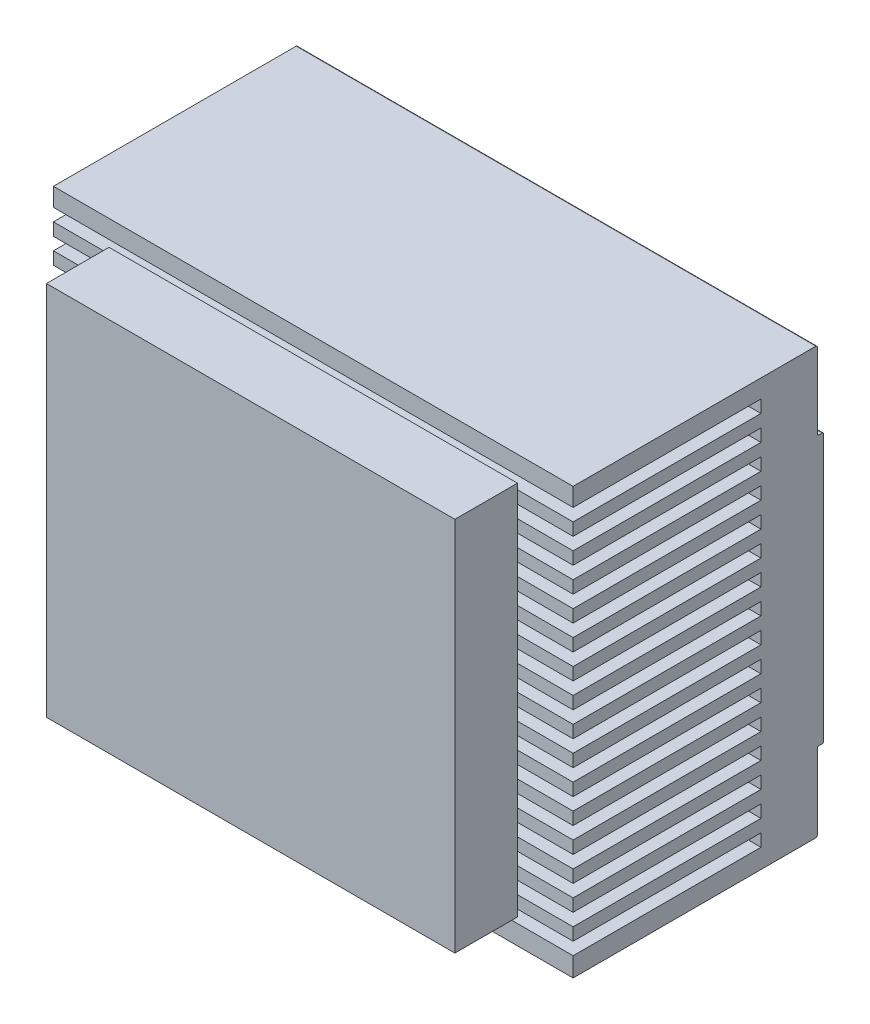
SolidWorks part; units mm, degrees
ref_plane "Front Plane" through (0, 0, 0) normal (0, 0, 1) x (1, 0, 0)
ref_plane "Top Plane" through (0, 0, 0) normal (0, 1, 0) x (1, 0, 0)
ref_plane "Right Plane" through (0, 0, 0) normal (1, 0, 0) x (0, 0, -1)
sketch "Sketch1" plane through (0, 0, 0) normal (0, 0, 1) x (1, 0, 0)
  line L1 (0, 0) -> (83, 0)
  line L2 (0, 0) -> (0, 68)
  line L3 (0, 68) -> (83, 68)
  line L4 (83, 0) -> (83, 68)
  dimension "D1" = 83
  dimension "D2" = 68
extrude "Boss-Extrude1" add sketch "Sketch1" along normal blind 40
sketch "Sketch2" plane through (0, 0, 40) normal (0, 0, 1) x (1, 0, 0)
  line L0 (8.8849, 64) -> (0, 68) construction
  line L1 (8.8849, 64) -> (74.1151, 64)
  line L2 (8.8849, 64) -> (8.8849, 4)
  line L3 (8.8849, 4) -> (74.1151, 4)
  line L4 (74.1151, 64) -> (74.1151, 4)
  line L5 (74.1151, 4) -> (83, 0) construction
  dimension "D1" = 60
extrude "Boss-Extrude2" add sketch "Sketch2" along normal blind 10 separate body
sketch "Sketch3" plane through (0, 0, 40) normal (0, 0, 1) x (1, 0, 0)
  line L0 (0, 68) -> (0, 0) construction
  line L1 (0, 65.0818) -> (83, 65.0818)
  line L2 (0, 65.0818) -> (0, 63.0818)
  line L3 (0, 63.0818) -> (83, 63.0818)
  line L4 (83, 65.0818) -> (83, 63.0818)
  line L5 (83, 0) -> (83, 68) construction
  line L6 (0, 61.0818) -> (0, 59.0818)
  line L7 (0, 61.0818) -> (83, 61.0818)
  line L8 (83, 61.0818) -> (83, 59.0818)
  line L9 (0, 59.0818) -> (83, 59.0818)
  line L10 (0, 57.0818) -> (0, 55.0818)
  line L11 (0, 57.0818) -> (83, 57.0818)
  line L12 (83, 57.0818) -> (83, 55.0818)
  line L13 (0, 55.0818) -> (83, 55.0818)
  line L14 (0, 53.0818) -> (0, 51.0818)
  line L15 (0, 53.0818) -> (83, 53.0818)
  line L16 (83, 53.0818) -> (83, 51.0818)
  line L17 (0, 51.0818) -> (83, 51.0818)
  line L18 (0, 49.0818) -> (0, 47.0818)
  line L19 (0, 49.0818) -> (83, 49.0818)
  line L20 (83, 49.0818) -> (83, 47.0818)
  line L21 (0, 47.0818) -> (83, 47.0818)
  line L22 (0, 45.0818) -> (0, 43.0818)
  line L23 (0, 45.0818) -> (83, 45.0818)
  line L24 (83, 45.0818) -> (83, 43.0818)
  line L25 (0, 43.0818) -> (83, 43.0818)
  line L26 (0, 41.0818) -> (0, 39.0818)
  line L27 (0, 41.0818) -> (83, 41.0818)
  line L28 (83, 41.0818) -> (83, 39.0818)
  line L29 (0, 39.0818) -> (83, 39.0818)
  line L30 (0, 37.0818) -> (0, 35.0818)
  line L31 (0, 37.0818) -> (83, 37.0818)
  line L32 (83, 37.0818) -> (83, 35.0818)
  line L33 (0, 35.0818) -> (83, 35.0818)
  line L34 (0, 33.0818) -> (0, 31.0818)
  line L35 (0, 33.0818) -> (83, 33.0818)
  line L36 (83, 33.0818) -> (83, 31.0818)
  line L37 (0, 31.0818) -> (83, 31.0818)
  line L38 (0, 29.0818) -> (0, 27.0818)
  line L39 (0, 29.0818) -> (83, 29.0818)
  line L40 (83, 29.0818) -> (83, 27.0818)
  line L41 (0, 27.0818) -> (83, 27.0818)
  line L42 (0, 25.0818) -> (0, 23.0818)
  line L43 (0, 25.0818) -> (83, 25.0818)
  line L44 (83, 25.0818) -> (83, 23.0818)
  line L45 (0, 23.0818) -> (83, 23.0818)
  line L46 (0, 21.0818) -> (0, 19.0818)
  line L47 (0, 21.0818) -> (83, 21.0818)
  line L48 (83, 21.0818) -> (83, 19.0818)
  line L49 (0, 19.0818) -> (83, 19.0818)
  line L50 (0, 17.0818) -> (0, 15.0818)
  line L51 (0, 17.0818) -> (83, 17.0818)
  line L52 (83, 17.0818) -> (83, 15.0818)
  line L53 (0, 15.0818) -> (83, 15.0818)
  line L54 (0, 13.0818) -> (0, 11.0818)
  line L55 (0, 13.0818) -> (83, 13.0818)
  line L56 (83, 13.0818) -> (83, 11.0818)
  line L57 (0, 11.0818) -> (83, 11.0818)
  line L58 (0, 9.0818) -> (0, 7.0818)
  line L59 (0, 9.0818) -> (83, 9.0818)
  line L60 (83, 9.0818) -> (83, 7.0818)
  line L61 (0, 7.0818) -> (83, 7.0818)
  line L62 (0, 5.0818) -> (0, 3.0818)
  line L63 (0, 5.0818) -> (83, 5.0818)
  line L64 (83, 5.0818) -> (83, 3.0818)
  line L65 (0, 3.0818) -> (83, 3.0818)
  dimension "D1" = 2
  dimension "D2" = 16
extrude "Cut-Extrude1" cut sketch "Sketch3" against normal offset from surface (30 mm away) 10 up to face at (41.5, 34, 0)
sketch "Sketch4" plane through (0, 0, 0) normal (0, 0, -1) x (-1, 0, 0)
  line L0 (0, 68) -> (0, 0) construction
  line L1 (-83, 68) -> (0, 68)
  line L2 (-83, 68) -> (-83, 55.5)
  line L3 (-83, 55.5) -> (0, 55.5)
  line L4 (0, 68) -> (0, 55.5)
  line L5 (-83, 0) -> (-83, 68) construction
  line L6 (0, 0) -> (-83, 0)
  line L7 (0, 0) -> (0, 12.5)
  line L8 (0, 12.5) -> (-83, 12.5)
  line L9 (-83, 0) -> (-83, 12.5)
  dimension "D1" = 12.5
  dimension "D2" = 12.5
extrude "Cut-Extrude2" cut sketch "Sketch4" against normal offset from surface (1 mm away) 1 up to face at (41.5, 34, 0)
fillet "Fillet1" radius 0.25 6 edges at (41.5, 0, 1) (41.5, 12.5, 0) (41.5, 12.5, 1) (41.5, 55.5, 1) (41.5, 55.5, 0) (41.5, 68, 1)
